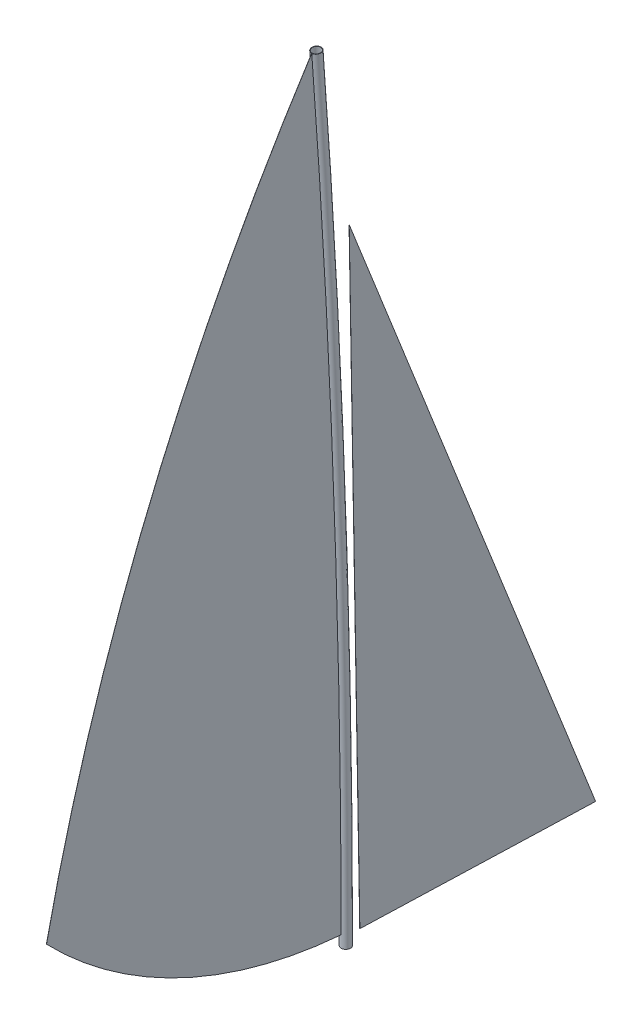
SolidWorks part; units mm, degrees
ref_plane "Спереди" through (0, 0, 0) normal (0, 0, 1) x (1, 0, 0)
ref_plane "Сверху" through (0, 0, 0) normal (0, 1, 0) x (1, 0, 0)
ref_plane "Справа" through (0, 0, 0) normal (1, 0, 0) x (0, 0, -1)
sketch "Эскиз1" plane through (0, 0, 0) normal (0, 1, 0) x (1, 0, 0)
  circle A0 centre (0, 0) radius 40
  dimension "D1" = 80
sketch "Эскиз3" plane through (0, 0, 0) normal (1, 0, 0) x (0, 0, -1)
  line L0 (0, 0) -> (0, 6700) construction
  line L1 (0, 6700) -> (-250, 6700) construction
  arc A0 (0, 0) -> (-250, 6700) centre (-89905, 0) ccw
  dimension "D1" = 6700
  dimension "D2" = 250
sweep "По траектории-Тонкостенный1" add profiles "Эскиз1" path "Эскиз3" parameters "D1"=3
sketch "Эскиз4" plane through (0, 0, 0) normal (1, 0, 0) x (0, 0, -1)
  line L0 (-2539.1213, 1279.7814) -> (-46.5732, 1086.8993) construction
  line L1 (-141.1328, 5705.3628) -> (2150, -83.8538) construction
  line L2 (27.187, 5280.0537) -> (2116.5802, 0.5911)
  line L3 (2116.5802, 0.5911) -> (117.6377, 65.6201)
  line L4 (117.6377, 65.6201) -> (27.187, 5280.0537)
  arc A0 (40, 0) -> (-210.1112, 6702.9809) centre (-89905, 0) ccw
  arc A1 (-40, 0) -> (-289.8888, 6697.0191) centre (-89905, 0) ccw
  arc A2 (-40.0556, 100) -> (-289.8888, 6697.0191) centre (-89905, 0) ccw
  arc A3 (40, 0) -> (-210.1112, 6702.9809) centre (-89905, 0) ccw construction
  arc A4 (-289.8888, 6697.0191) -> (-2539.1213, 1279.7814) centre (13453.4213, -2184.7504) ccw
  arc A5 (-40.0556, 100) -> (-2539.1213, 1279.7814) centre (273.233, 4000.329) cw
  arc A6 (-40, 0) -> (-40.0556, 100) centre (-89905, 0) ccw construction
  arc A7 (40, 0) -> (-210.1112, 6702.9809) centre (-89905, 0) ccw construction
  spline S0 degree 3 poles (2300, -93.2931) (1859.2294, -64.8665) (1417.9017, -42.4845) (565.7086, -11.0039) (154.8849, -1.0813) (-256.0036, 3.5901) knots 0.517592 0.517592 0.517592 0.517592 0.767592 0.767592 1 1 1 1 construction
  point P14 (2100, 0)
  dimension "D1" = 2500
  dimension "D2" = 100
  dimension "D3" = 1000
  dimension "D4" = 2150
  dimension "D5" = 2000
extrude "Бобышка-Вытянуть1" add sketch "Эскиз4" along normal blind 1 separate body
